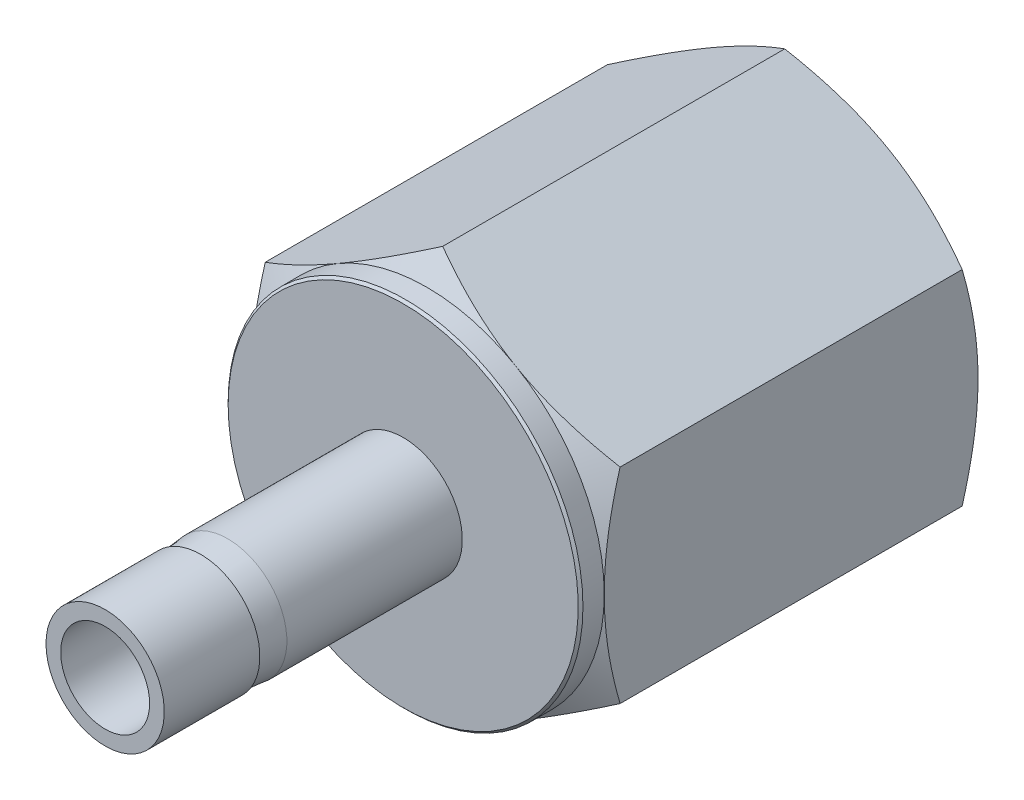
SolidWorks part; units mm, degrees
material "AISI 316 Stainless Steel Sheet (SS)"
ref_plane "Front Plane" through (0, 0, 0) normal (0, 0, 1) x (1, 0, 0)
ref_plane "Top Plane" through (0, 0, 0) normal (0, 1, 0) x (1, 0, 0)
ref_plane "Right Plane" through (0, 0, 0) normal (1, 0, 0) x (0, 0, -1)
sketch "Sketch1" plane through (0, 0, 0) normal (1, 0, 0) x (0, 0, -1)
  line L0 (0, 0) -> (37.338, 0) construction
  line L4 (0, 3.175) -> (0, -3.175) construction
  line L5 (16.002, 9.525) -> (16.002, -9.525) construction
  line L7 (0, 3.175) -> (5.1308, 3.175) construction
  line L14 (0, 2.3876) -> (0, -2.3876) construction
  line L21 (37.338, 6.858) -> (37.338, -6.858) construction
  line L22 (22.2352, 6.3878) -> (22.2352, -6.3878) construction
  line L23 (22.2352, 6.3878) -> (37.338, 6.858) construction
  line L24 (22.2352, 6.3878) -> (22.2352, 4.9767) construction
  line L25 (27.1323, 6.5402) -> (27.1323, -6.5402) construction
  line L26 (37.338, 4.6228) -> (37.338, -4.6228) construction
  point P15 (16.002, 0)
  point P33 (0, 0)
  point P40 (22.2352, 0)
  point P44 (27.1323, 0)
sketch "Sketch2" plane through (0, 0, 0) normal (1, 0, 0) x (0, 0, -1)
  line L0 (5.1308, 3.175) -> (5.1308, 3.048)
  line L1 (16.002, 0) -> (0, 0)
  line L2 (16.002, 0) -> (16.002, 3.175)
  line L3 (16.002, 3.175) -> (6.5824, 3.175)
  line L4 (0, 0) -> (0, 3.175)
  line L5 (5.1308, 3.048) -> (6.5824, 3.175)
  line L6 (5.1308, 3.175) -> (0, 3.175)
  dimension "D1" = 5
  dimension "D2" = 0.127
revolve "Revolve1" add sketch "Sketch2" angle 360 about L1
sketch "Sketch3" plane through (0, 0, -16.002) normal (0, 0, -1) x (-1, 0, 0)
  line L0 (0, 0) -> (0, 10.9985) construction
  line L1 (0, 10.9985) -> (-9.525, 5.4993)
  line L2 (-9.525, 5.4993) -> (-9.525, -5.4993)
  line L3 (-9.525, -5.4993) -> (0, -10.9985)
  line L4 (0, -10.9985) -> (9.525, -5.4993)
  line L5 (9.525, -5.4993) -> (9.525, 5.4993)
  line L6 (9.525, 5.4993) -> (0, 10.9985)
  circle A0 centre (0, 0) radius 9.525 construction
extrude "Boss-Extrude1" add sketch "Sketch3" along normal up to vertex (21.336 mm away) up to point (0, 0, -37.338)
sketch "Sketch4" plane through (0, 0, 0) normal (1, 0, 0) x (0, 0, -1)
  line L0 (37.338, 10.9985) -> (16.002, 10.9985) construction
  line L1 (37.338, 10.9985) -> (37.338, 5.4993) construction
  line L2 (16.002, 10.9985) -> (16.002, 9.525)
  line L3 (16.002, 10.9985) -> (16.002, 5.4993) construction
  line L4 (16.002, 9.525) -> (17.272, 9.525)
  line L5 (18.1227, 10.9985) -> (36.4873, 10.9985)
  line L6 (17.272, 9.525) -> (18.1227, 10.9985)
  line L7 (37.338, 9.525) -> (36.4873, 10.9985)
  line L8 (37.338, 10.9985) -> (37.338, 5.4993) construction
  line L9 (17.272, 9.525) -> (17.272, 10.9985) construction
  line L11 (0, 0) -> (37.338, 0)
  line L12 (0, 0) -> (0, 2.3876)
  line L13 (0, 2.3876) -> (37.338, 2.3876)
  line L14 (16.002, 10.9985) -> (16.002, 12.472)
  line L15 (16.002, 12.472) -> (37.338, 12.472)
  line L16 (37.338, 12.472) -> (37.338, 10.9985)
  line L17 (37.338, 10.9985) -> (37.338, 9.525)
  line L18 (37.338, 0) -> (37.338, 2.3876)
  dimension "D1" = 30
  dimension "D2" = 1.27
revolve "Cut-Revolve1" cut sketch "Sketch4" angle 360 about L0
chamfer "Chamfer1" distance 0.127 angle 45 1 edges at (-9.525, 0, -16.002)
sketch "Sketch5" plane through (0, 0, 0) normal (1, 0, 0) x (0, 0, -1)
  line L0 (27.1323, 0) -> (37.338, 0)
  line L1 (37.338, 0) -> (37.338, 6.858)
  line L2 (37.338, 6.858) -> (27.1323, 6.5402)
  line L3 (27.1323, 6.5402) -> (27.1323, 0)
revolve "Revolve2" add sketch "Sketch5" angle 360 about L0
sketch "Sketch6" plane through (0, 0, -37.338) normal (0, 0, -1) x (-1, 0, 0)
  circle A1 centre (0, 0) radius 6.858
  circle A2 centre (0, 0) radius 6.858
  point P0 (0, 6.858)
  dimension "D1" = 0
curve "Helix/Spiral1"
sketch "Sketch7" plane through (0, 0, 0) normal (1, 0, 0) x (0, 0, -1)
  line L0 (37.2498, 7.0108) -> (38.6609, 7.0108) construction
  line L1 (37.2498, 7.0108) -> (37.9554, 5.7887) construction
  line L2 (37.9554, 5.7887) -> (38.6609, 7.0108) construction
  line L3 (37.8672, 5.9415) -> (38.0436, 5.9415) construction
  line L4 (37.338, 6.858) -> (38.5727, 6.858) construction
  line L5 (37.9554, 5.7887) -> (37.9554, 5.9415) construction
  line L6 (37.9554, 6.858) -> (37.9554, 7.0108) construction
  line L7 (37.9554, 6.9344) -> (38.6168, 6.9344) construction
  line L8 (37.9554, 5.7887) -> (37.9554, -6.8772) construction
  line L9 (37.9554, -6.8772) -> (36.5449, -6.8333) construction
  line L10 (36.5449, -6.8333) -> (35.1345, -6.7894) construction
  line L11 (35.1345, -6.7894) -> (33.7241, -6.7455) construction
  line L12 (37.2498, 7.0108) -> (38.6168, 6.9344)
  line L13 (38.6168, 6.9344) -> (38.0436, 5.9415)
  line L14 (38.0436, 5.9415) -> (37.8672, 5.9415)
  line L15 (37.8672, 5.9415) -> (37.2498, 7.0108)
  line L16 (27.1323, -6.5402) -> (37.338, -6.858) construction
  line L17 (33.7241, -6.7455) -> (32.3137, -6.7016) construction
  line L18 (32.3137, -6.7016) -> (30.9032, -6.6577) construction
  dimension "D1" = 1.4111
  dimension "D2" = 0.1764
sweep "Cut-Sweep1" cut profiles "Sketch7" path "Helix/Spiral1"
combine bodies "Combine1" operation type subtract main body 113 bodies to subtract 122
sketch "Sketch8" plane through (0, 0, 0) normal (1, 0, 0) x (0, 0, -1)
  line L0 (37.9554, 5.7887) -> (37.338, 5.7887) construction
  line L1 (37.338, 7.0108) -> (36.1159, 5.7887)
  line L2 (36.1159, 5.7887) -> (37.338, 5.7887)
  line L5 (37.338, 6.858) -> (37.338, -6.858) construction
  line L8 (37.338, 7.0108) -> (37.338, 5.7887)
  line L9 (37.2498, 7.0108) -> (38.6609, 7.0108) construction
  line L10 (37.338, 4.6228) -> (22.2352, 4.6228)
  line L11 (22.2352, 4.6228) -> (22.2352, 0) construction
  line L12 (19.4575, 0) -> (37.338, 0)
  line L13 (19.4575, 0) -> (22.2352, 4.6228)
  line L14 (37.338, 0) -> (37.338, 4.6228)
  dimension "D1" = 59
revolve "Cut-Revolve2" cut sketch "Sketch8" angle 360 about L0
equation "\"D4@Helix/Spiral1\" = \"Pipe Pitch@Sketch1\""
equation "\"D3@Helix/Spiral1\" = \"D4@Helix/Spiral1\" + \"L4@Sketch1\""
equation "\"D1@Sketch7\" = \"D4@Helix/Spiral1\""
equation "\"D2@Sketch7\" = \"D1@Sketch7\" / 8"
